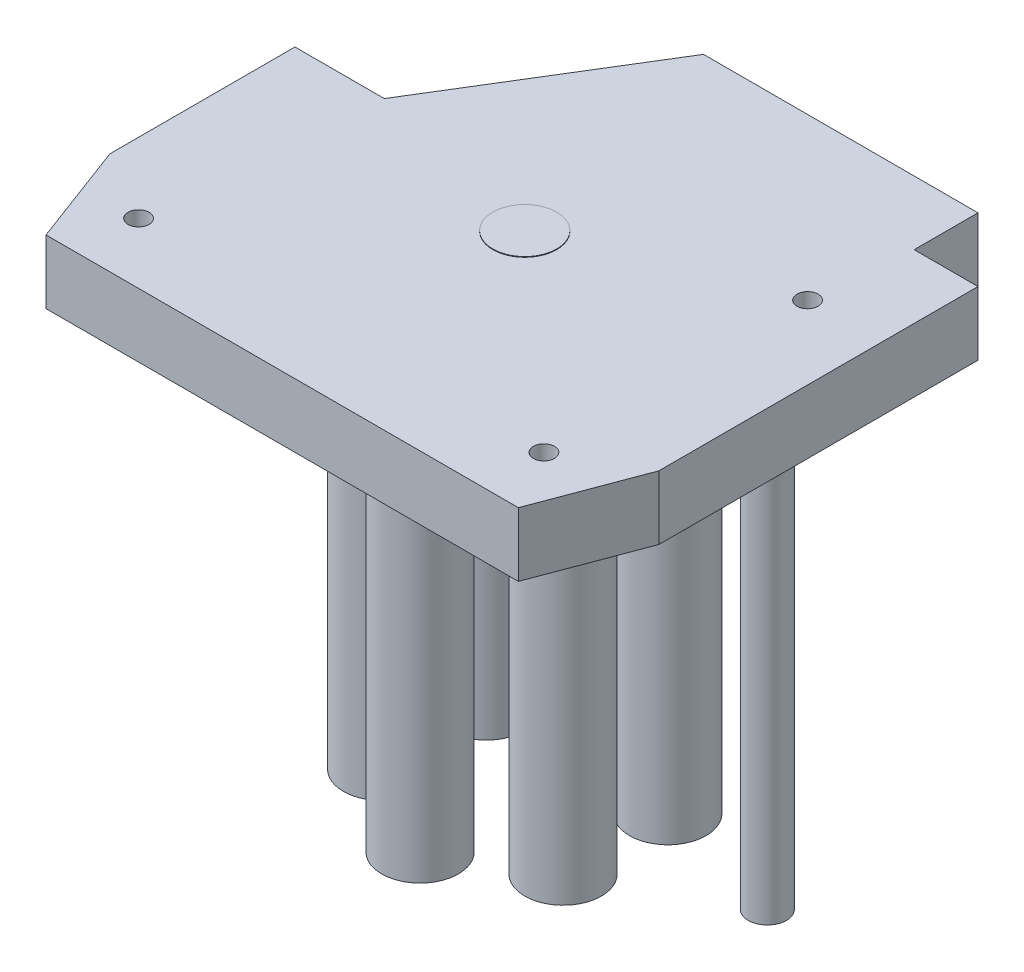
SolidWorks part; units mm, degrees
ref_plane "Front Plane" through (0, 0, 0) normal (0, 0, 1) x (1, 0, 0)
ref_plane "Top Plane" through (0, 0, 0) normal (0, 1, 0) x (1, 0, 0)
ref_plane "Right Plane" through (0, 0, 0) normal (1, 0, 0) x (0, 0, -1)
sketch "Sketch1" plane through (0, 0, 0) normal (0, 1, 0) x (1, 0, 0)
  line L0 (0, 0) -> (0, -45)
  line L1 (0, -45) -> (86, -45)
  line L2 (86, -45) -> (86, 31)
  line L3 (86, 31) -> (33, 31)
  line L4 (33, 31) -> (14, 0)
  line L5 (14, 0) -> (0, 0)
  dimension "D1" = 86
  dimension "D2" = 76
  dimension "D3" = 14
  dimension "D4" = 45
  dimension "D5" = 53
extrude "Boss-Extrude1" add sketch "Sketch1" along normal blind 10
chamfer "Chamfer1" distance 6 distance2 16 1 edges at (86, 5, 45)
chamfer "Chamfer2" distance 16 distance2 6 1 edges at (0, 5, 45)
sketch "Sketch2" plane through (0, 10, 0) normal (0, 1, 0) x (1, 0, 0)
  line L1 (86, 31) -> (76, 31)
  line L2 (86, 31) -> (86, 21)
  line L3 (86, 21) -> (76, 21)
  line L4 (76, 31) -> (76, 21)
  dimension "D1" = 10
  dimension "D2" = 10
extrude "Cut-Extrude1" cut sketch "Sketch2" against normal blind 10
sketch "Sketch3" plane through (0, 10, 0) normal (0, 1, 0) x (1, 0, 0)
  line L0 (76, 31) -> (33, 31) construction
  line L1 (86, -29) -> (86, 21) construction
  line L3 (43, -7) -> (43, 1.8763) construction
  arc A0 (41.3, -2.2979) -> (44.7, -2.2979) centre (43, -7) ccw
  arc A1 (44.7, -2.2979) -> (41.3, -2.2979) centre (43, -7) ccw
  dimension "D1" = 38
  dimension "D2" = 43
  dimension "D4" = 5
extrude "Boss-Extrude2" add sketch "Sketch3" along normal blind 0.1
sketch "Sketch4" plane through (0, 10, 0) normal (0, 1, 0) x (1, 0, 0)
  circle A0 centre (43, -7) radius 16.4 construction
  circle A1 centre (43, 9.4) radius 6
  circle A2 centre (57.2028, 1.2) radius 6
  circle A3 centre (57.2028, -15.2) radius 6
  circle A4 centre (43, -23.4) radius 6
  circle A5 centre (28.7972, -15.2) radius 6
  circle A6 centre (28.7972, 1.2) radius 6
  point P18 (43, -7)
  dimension "D1" = 32.8
  dimension "D2" = 12
  dimension "D3" = 6
extrude "Boss-Extrude3" add sketch "Sketch4" against normal up to surface (76 mm away)
sketch "Sketch5" plane through (0, 10, 0) normal (0, 1, 0) x (1, 0, 0)
  line L0 (76, 31) -> (33, 31) construction
  line L1 (86, -29) -> (86, 21) construction
  circle A0 centre (78, -4) radius 3
  dimension "D1" = 6
  dimension "D2" = 35
  dimension "D3" = 8
extrude "Boss-Extrude4" add sketch "Sketch5" against normal up to surface (76 mm away)
sketch "Sketch6" plane through (0, 0, 0) normal (0, -1, 0) x (1, 0, 0)
  circle A0 centre (74.5, -5.8) radius 1.65
  circle A1 centre (74.5, 35.5) radius 1.65
  circle A2 centre (11, 35.5) radius 1.65
  dimension "D1" = 3.3
extrude "Cut-Extrude2" cut sketch "Sketch6" against normal through all
sketch "Sketch7" plane through (0, 0, -31) normal (0, 0, -1) x (-1, 0, 0)
  line L0 (-86, 0) -> (-86, 10) construction
  line L1 (-76, 10) -> (-33, 10) construction
  circle A0 centre (-43, 5) radius 1.65
  dimension "D1" = 43
  dimension "D2" = 3.3
  dimension "D3" = 5
extrude "Cut-Extrude3" cut sketch "Sketch7" against normal blind 10
